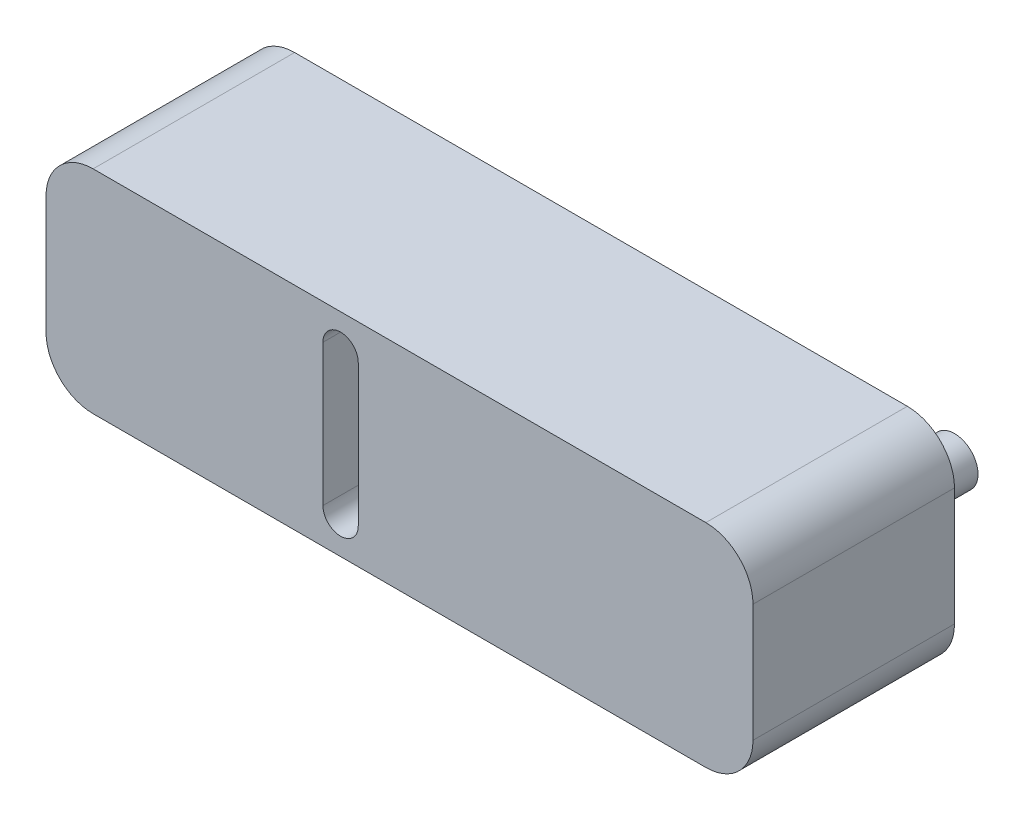
SolidWorks part; units mm, degrees
material "Cast Alloy Steel"
ref_plane "Front Plane" through (0, 0, 0) normal (0, 0, 1) x (1, 0, 0)
ref_plane "Top Plane" through (0, 0, 0) normal (0, 1, 0) x (1, 0, 0)
ref_plane "Right Plane" through (0, 0, 0) normal (1, 0, 0) x (0, 0, -1)
sketch "Sketch1" plane through (0, 0, 0) normal (0, 0, 1) x (1, 0, 0)
  line L1 (-38.1, -11.43) -> (38.1, -11.43)
  line L2 (-38.1, -11.43) -> (-38.1, 11.43)
  line L3 (-38.1, 11.43) -> (38.1, 11.43)
  line L4 (38.1, -11.43) -> (38.1, 11.43)
  line L5 (-38.1, -11.43) -> (38.1, 11.43) construction
  line L6 (-38.1, 11.43) -> (38.1, -11.43) construction
  point P0 (0, 0)
  dimension "D1" = 76.2
  dimension "D2" = 22.86
extrude "Boss-Extrude1" add sketch "Sketch1" against normal blind 21.717
sketch "Sketch2" plane through (0, 0, 0) normal (0, 0, 1) x (1, 0, 0)
  line L0 (-38.1, -7.62) -> (-6.35, -7.62) construction
  line L1 (-38.1, 11.43) -> (-38.1, -11.43) construction
  line L2 (-6.35, -7.62) -> (-6.35, -11.43) construction
  line L7 (-38.1, -11.43) -> (38.1, -11.43) construction
  line L8 (0, 0) -> (-38.1, 0) construction
  line L9 (-6.35, -7.62) -> (-6.35, 7.62) construction
  line L10 (-8.255, -7.62) -> (-8.255, 7.62)
  line L11 (-4.445, -7.62) -> (-4.445, 7.62)
  line L12 (-6.35, 7.62) -> (-6.35, 11.43) construction
  line L13 (-38.1, 7.62) -> (-6.35, 7.62) construction
  arc A2 (-8.255, -7.62) -> (-4.445, -7.62) centre (-6.35, -7.62) ccw
  arc A3 (-4.445, 7.62) -> (-8.255, 7.62) centre (-6.35, 7.62) ccw
  point P9 (-6.35, 0)
  point P19 (0, 0)
  dimension "D2" = 3.81
  dimension "D3" = 1.905
  dimension "D1" = 31.75
extrude "Cut-Extrude3" cut sketch "Sketch2" against normal up to next
fillet "Fillet1" radius 5.08 4 edges at (38.1, -11.43, -10.8585) (-38.1, -11.43, -10.8585) (-38.1, 11.43, -10.8585) (38.1, 11.43, -10.8585)
sketch "Sketch3" plane through (0, 0, -21.717) normal (0, 0, -1) x (-1, 0, 0)
  line L0 (-38.1, 0) -> (-29.21, 0) construction
  line L1 (-38.1, -6.35) -> (-38.1, 6.35) construction
  circle A0 centre (-29.21, 0) radius 2.54
  dimension "D2" = 5.08
  dimension "D1" = 8.89
extrude "Boss-Extrude2" add sketch "Sketch3" along normal blind 8.89
